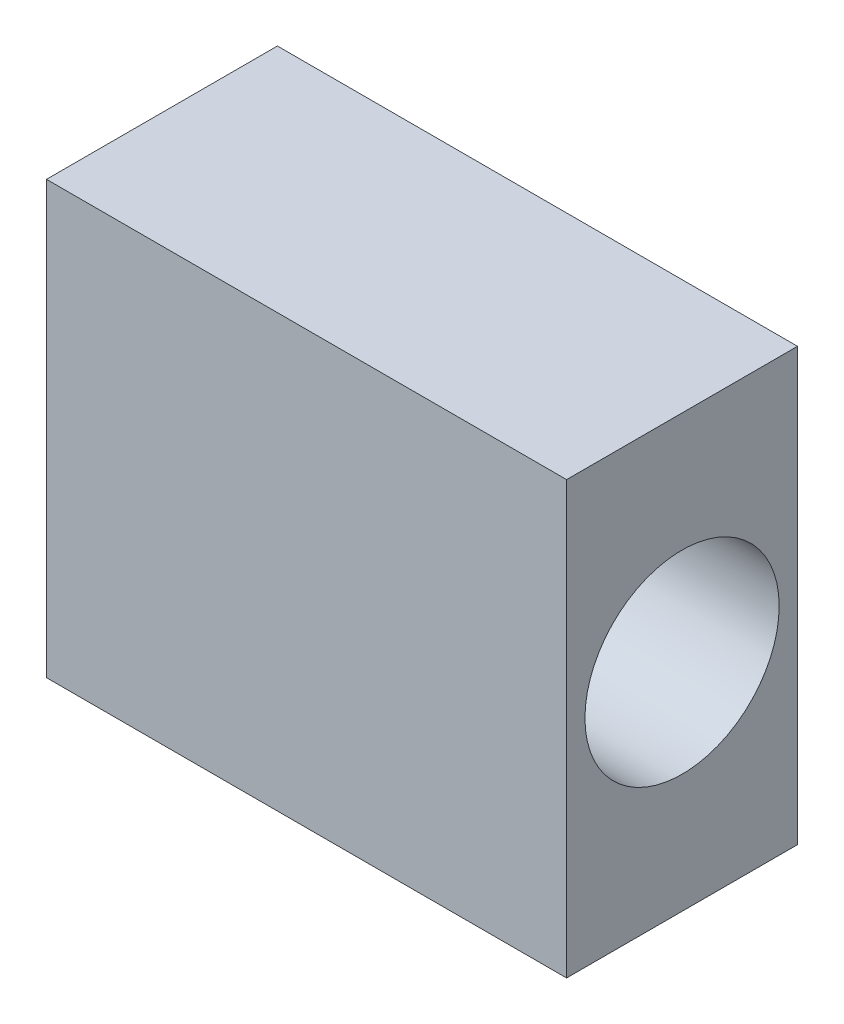
SolidWorks part; units mm, degrees
ref_plane "Front Plane" through (0, 0, 0) normal (0, 0, 1) x (1, 0, 0)
ref_plane "Top Plane" through (0, 0, 0) normal (0, 1, 0) x (1, 0, 0)
ref_plane "Right Plane" through (0, 0, 0) normal (1, 0, 0) x (0, 0, -1)
sketch "Sketch1" plane through (0, 0, 0) normal (0, 1, 0) x (1, 0, 0)
  line L1 (0, 0) -> (12.05, 0)
  line L2 (0, 0) -> (0, 5.35)
  line L3 (0, 5.35) -> (12.05, 5.35)
  line L4 (12.05, 0) -> (12.05, 5.35)
  dimension "D1" = 12.05
  dimension "D2" = 5.35
extrude "Boss-Extrude1" add sketch "Sketch1" along normal blind 10
sketch "Sketch3" plane through (0, 0, 0) normal (-1, 0, 0) x (0, 0, 1)
  line L0 (-5.35, 10) -> (0, 10) construction
  line L1 (-5.35, 10) -> (-5.35, 0) construction
  circle A0 centre (-2.675, 5) radius 2.25
  point P2 (0, 0)
  point P5 (-2.675, 10)
  point P8 (-5.35, 5)
  dimension "D1" = 4.5
extrude "Cut-Extrude2" cut sketch "Sketch3" against normal up to surface (12.05 mm away) up to face at (12.05, 5, -2.675)
